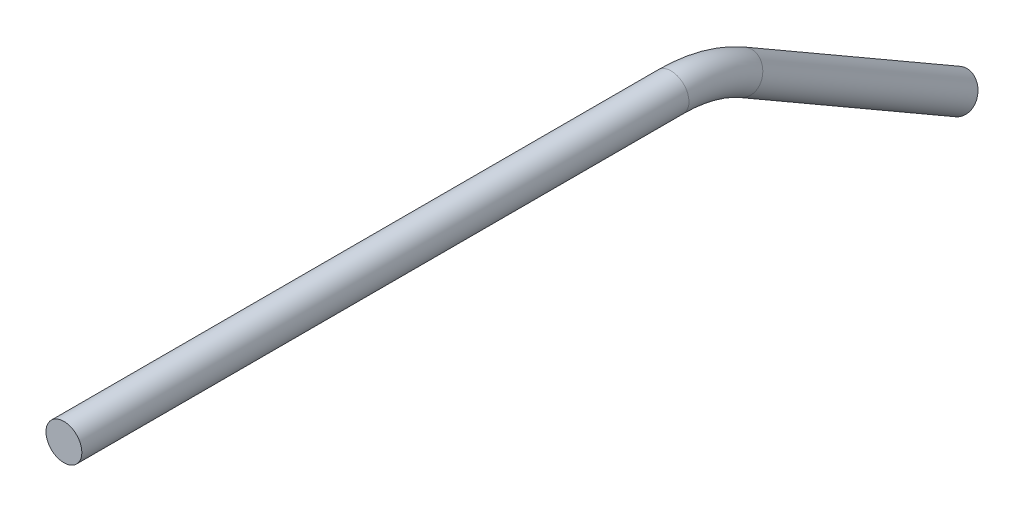
SolidWorks part; units mm, degrees
ref_plane "Front Plane" through (0, 0, 0) normal (0, 0, 1) x (1, 0, 0)
ref_plane "Top Plane" through (0, 0, 0) normal (0, 1, 0) x (1, 0, 0)
ref_plane "Right Plane" through (0, 0, 0) normal (1, 0, 0) x (0, 0, -1)
sketch "Sketch2" plane through (0, 0, 0) normal (0, 0, 1) x (1, 0, 0)
  circle A0 centre (0, 0) radius 3.175
  dimension "D1" = 6.35
sketch "Sketch4" plane through (0, 0, 0) normal (1, 0, 0) x (0, 0, -1)
  line L0 (0, 0) -> (107.4941, 0)
  line L1 (120.1941, -3.403) -> (158.2941, -25.4)
  arc A0 (120.1941, -3.403) -> (107.4941, 0) centre (107.4941, -25.4) ccw
  point P6 (114.3, 0)
  dimension "D4" = 25.4
  dimension "D1" = 114.3
  dimension "D2" = 50.8
  dimension "D3" = 30
sweep "Sweep1" add profiles "Sketch2" path "Sketch4"
